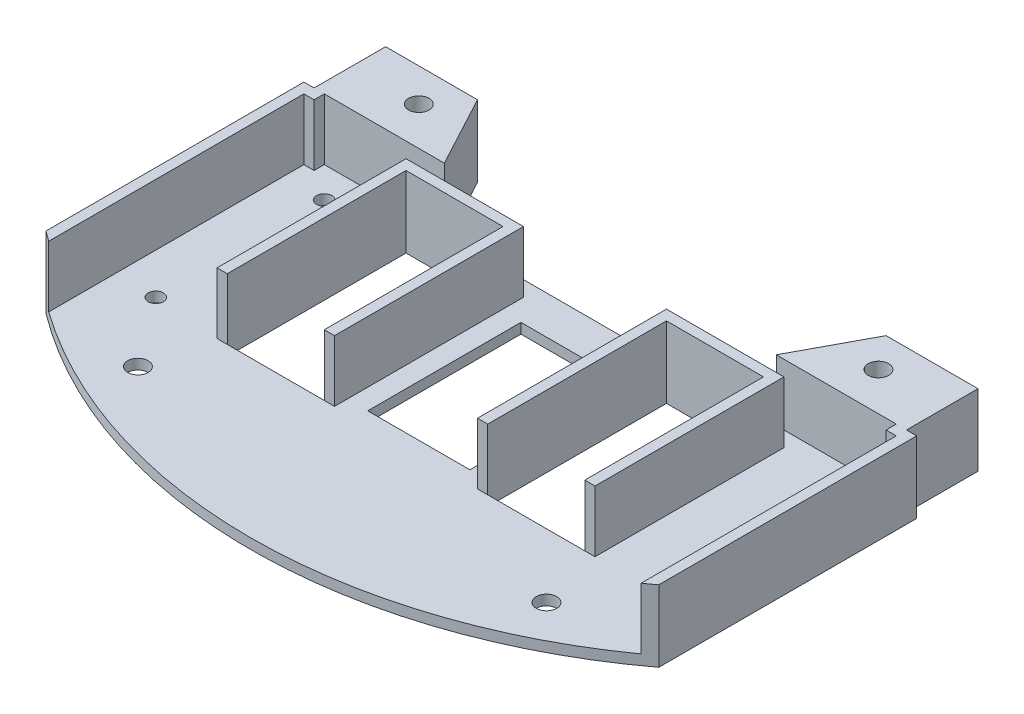
SolidWorks part; units mm, degrees
ref_plane "前视基准面" through (0, 0, 0) normal (0, 0, 1) x (1, 0, 0)
ref_plane "上视基准面" through (0, 0, 0) normal (0, 1, 0) x (1, 0, 0)
ref_plane "右视基准面" through (0, 0, 0) normal (1, 0, 0) x (0, 0, -1)
sketch "草图1" plane through (0, 0, 0) normal (0, 1, 0) x (1, 0, 0)
  line L0 (-60, -80) -> (-60, 80)
  line L1 (0, 23.6809) -> (0, 56.992)
  line L2 (60, -80) -> (60, 80)
  line L3 (-60, -29.5) -> (60, -29.5)
  line L5 (-58, -29.5) -> (58, -29.5)
  line L6 (-58, -29.5) -> (-58, -15.5)
  line L7 (-58, -15.5) -> (58, -15.5)
  line L8 (58, -29.5) -> (58, -15.5)
  circle A0 centre (0, 0) radius 100
  dimension "D1" = 200
  dimension "D2" = 60
  dimension "D3" = 29.5
  dimension "D4" = 2
  dimension "D5" = 2
  dimension "D6" = 15.5
extrude "底板" add sketch "草图1" along normal blind 2 contours L0 A0 L2 L3 | L3 L8 L7 L6
sketch "草图3" plane through (0, 2, 0) normal (0, 1, 0) x (1, 0, 0)
  line L0 (-40, -15.5) -> (40, -15.5)
  line L1 (-58, -15.5) -> (58, -15.5) construction
  line L2 (-32.5, -29.5) -> (32.5, -29.5)
  line L3 (-32.5, -29.5) -> (-40, -15.5)
  line L4 (40, -15.5) -> (32.5, -29.5)
  line L5 (58, -29.5) -> (60, -29.5) construction
  point P6 (0, -15.5)
  point P7 (0, -29.5)
  dimension "D1" = 0
  dimension "D2" = 0
  dimension "D3" = 80
  dimension "D4" = 65
  dimension "D5" = 0
extrude "大豁口" cut sketch "草图3" against normal blind 2
sketch "草图5" plane through (0, 2, 0) normal (0, 1, 0) x (1, 0, 0)
  line L0 (0, -70.6851) -> (0, -80.6851)
  line L1 (-35, -34.5) -> (-16, -34.5)
  line L2 (-35, -34.5) -> (-35, -69.5)
  line L3 (-35, -69.5) -> (-16, -69.5)
  line L4 (-16, -34.5) -> (-16, -69.5)
  line L5 (16, -34.5) -> (16, -69.5)
  line L6 (35, -69.5) -> (16, -69.5)
  line L7 (35, -34.5) -> (35, -69.5)
  line L8 (35, -34.5) -> (16, -34.5)
  line L10 (-10, -67) -> (10, -67)
  line L11 (-10, -67) -> (-10, -37)
  line L12 (-10, -37) -> (10, -37)
  line L13 (10, -67) -> (10, -37)
  line L14 (-10, -67) -> (10, -37) construction
  line L15 (-10, -37) -> (10, -67) construction
  point P7 (-16, -52)
  point P12 (0, -52)
  dimension "D1" = 52
  dimension "D2" = 19
  dimension "D3" = 16
  dimension "D4" = 52
  dimension "D5" = 35
  dimension "D6" = 30
  dimension "D7" = 20
extrude "散热口" cut sketch "草图5" against normal blind 2 contours L4 L1 L2 L3 | L7 L8 L5 L6 | L10 L13 L12 L11
sketch "草图6" plane through (0, 2, 0) normal (0, 1, 0) x (1, 0, 0)
  line L0 (-58, -29.5) -> (-58, -81.4616)
  line L1 (58, -29.5) -> (58, -81.4616)
  line L2 (0, -46.6621) -> (0, -61.7598)
  line L3 (-58, -29.5) -> (58, -29.5)
  line L4 (-35, -34.5) -> (-35, -69.5) construction
  line L5 (-37, -69.5) -> (-14, -69.5)
  line L6 (-37, -69.5) -> (-37, -32.5)
  line L7 (-37, -32.5) -> (-14, -32.5)
  line L8 (-14, -69.5) -> (-14, -32.5)
  line L9 (37, -69.5) -> (14, -69.5)
  line L10 (37, -69.5) -> (37, -32.5)
  line L11 (37, -32.5) -> (14, -32.5)
  line L12 (14, -69.5) -> (14, -32.5)
  line L13 (-16, -34.5) -> (-16, -69.5) construction
  line L14 (16, -34.5) -> (16, -69.5) construction
  line L15 (35, -34.5) -> (35, -69.5) construction
  line L16 (35, -34.5) -> (16, -34.5) construction
  line L17 (-35, -34.5) -> (-16, -34.5) construction
  arc A0 (-60, -80) -> (60, -80) centre (0, 0) ccw construction
  line M16 (-58, -29.5) -> (-60, -29.5)
  line M17 (-60, -29.5) -> (-60, -80)
  arc M18 (-60, -80) -> (60, -80) centre (0, 0) ccw
  line M19 (60, -80) -> (60, -29.5)
  line M20 (60, -29.5) -> (58, -29.5)
  line M25 (-35, -34.5) -> (-16, -34.5)
  line M26 (-16, -34.5) -> (-16, -69.5)
  line M28 (-35, -69.5) -> (-35, -34.5)
  line M29 (16, -34.5) -> (35, -34.5)
  line M30 (35, -34.5) -> (35, -69.5)
  line M32 (16, -69.5) -> (16, -34.5)
  dimension "D1" = 2
  dimension "D2" = 2
  dimension "D3" = 2
  dimension "D4" = 2
  dimension "D5" = 2
  dimension "D6" = 2
extrude "小支撑" add sketch "草图6" along normal blind 12 contours L0 M16 M17 M18 | L1 M20 M18 M19 | L5 L8 L7 L6 M28 M25 M26 | L12 L9 L10 L11 M32 M29 M30
sketch "草图7" plane through (0, 2, 0) normal (0, 1, 0) x (1, 0, 0)
  line L0 (-32.5, -29.5) -> (-58, -29.5)
  line L1 (32.5, -29.5) -> (58, -29.5)
  line L3 (-58, -29.5) -> (-56, -29.5)
  line L4 (-58, -29.5) -> (-58, -31.5)
  line L5 (-58, -31.5) -> (-56, -31.5)
  line L6 (-56, -29.5) -> (-56, -31.5)
  line L7 (58, -29.5) -> (56, -29.5)
  line L8 (58, -29.5) -> (58, -31.5)
  line L9 (58, -31.5) -> (56, -31.5)
  line L10 (56, -29.5) -> (56, -31.5)
  line M12 (58, -81.4616) -> (58, -29.5)
  line M13 (58, -29.5) -> (58, -15.5)
  line M14 (58, -15.5) -> (40, -15.5)
  line M15 (40, -15.5) -> (32.5, -29.5)
  line M17 (-32.5, -29.5) -> (-40, -15.5)
  line M18 (-40, -15.5) -> (-58, -15.5)
  line M19 (-58, -15.5) -> (-58, -29.5)
  line M20 (-58, -29.5) -> (-58, -81.4616)
  dimension "D1" = 2
  dimension "D2" = 2
  dimension "D3" = 2
  dimension "D4" = 2
extrude "大支撑" add sketch "草图7" along normal blind 12 contours L6 L0 L5 M20 | L0 M17 M18 M19 | L1 L10 L9 M12 | L1 M15 M13 M14
sketch "草图2" plane through (0, 2, 0) normal (0, 1, 0) x (1, 0, 0)
  line L0 (0, -32.9316) -> (0, -57.716)
  line L1 (-17.6648, -52) -> (18.2941, -52)
  circle A0 centre (-45, -22) radius 2
  circle A1 centre (-40, -82) radius 2
  circle A2 centre (40, -82) radius 2
  circle A3 centre (45, -22) radius 2
  circle A4 centre (-50, -35.5) radius 1.5
  circle A5 centre (-50, -68.5) radius 1.5
  circle A6 centre (50, -35.5) radius 1.5
  circle A7 centre (50, -68.5) radius 1.5
  dimension "D1" = 4
  dimension "D2" = 4
  dimension "D3" = 45
  dimension "D4" = 22
  dimension "D5" = 40
  dimension "D6" = 82
  dimension "D8" = 3
  dimension "D9" = 50
  dimension "D10" = 16.5
  dimension "D7" = 52
extrude "螺丝孔" cut sketch "草图2" against normal blind 2 and the other way blind 12 contours A0 | A1 | A2 | A3 | A4 | A5 | A7 | A6
